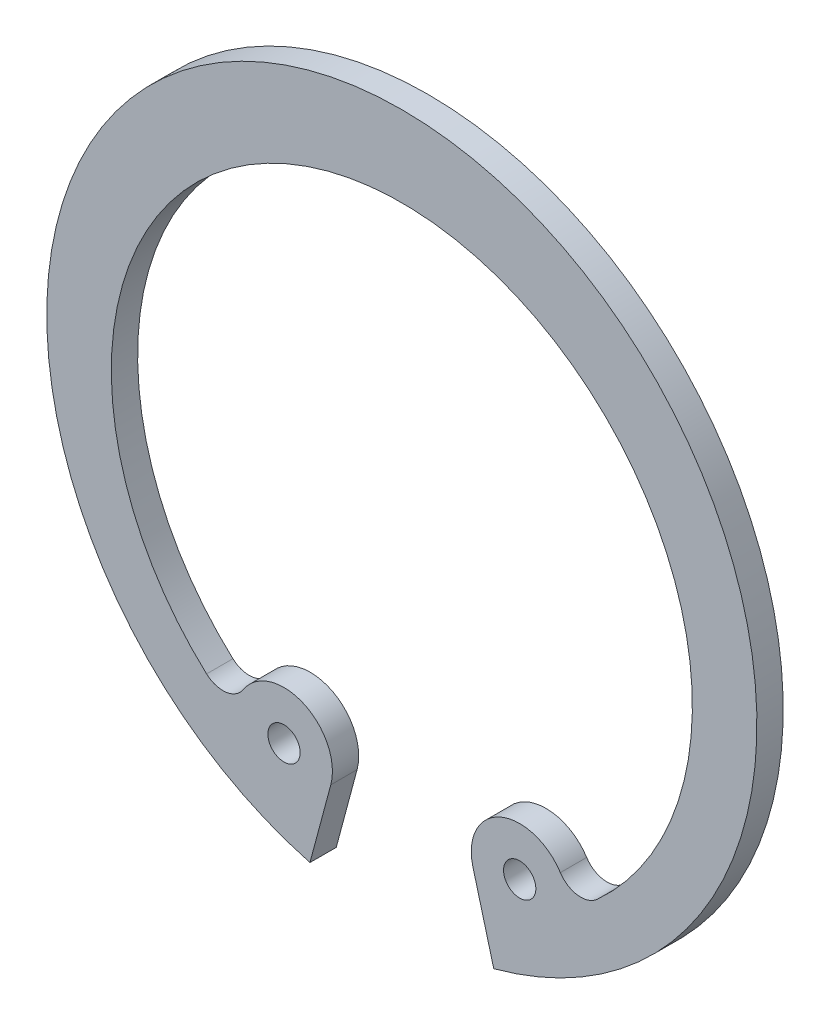
SolidWorks part; units mm, degrees
ref_plane "Face" through (0, 0, 0) normal (0, 0, 1) x (1, 0, 0)
ref_plane "Dessus" through (0, 0, 0) normal (0, 1, 0) x (1, 0, 0)
ref_plane "Droite" through (0, 0, 0) normal (1, 0, 0) x (0, 0, -1)
sketch "Esquisse1" plane through (0, 0, 0) normal (0, 0, 1) x (1, 0, 0)
  line L0 (0, 17) -> (0, -15) construction
  line L1 (-3.4941, -13.04) -> (-2.7022, -10.0846)
  line L2 (0, 0) -> (-9.5131, -9.5131) construction
  line L3 (0, 0) -> (-4.4803, -9.6081) construction
  line L4 (3.4941, -13.04) -> (2.7022, -10.0846)
  arc A0 (3.4941, -13.04) -> (-3.4941, -13.04) centre (0, 0) ccw
  arc A1 (7.4234, -8.7926) -> (-7.4234, -8.7926) centre (0, -0.6136) ccw
  circle A2 centre (-4.4803, -9.6081) radius 0.6136
  arc A3 (-2.7022, -10.0846) -> (-6.0269, -8.6096) centre (-4.4803, -9.6081) ccw
  arc A4 (-7.4234, -8.7926) -> (-6.0269, -8.6096) centre (-6.8028, -8.1088) ccw
  arc A5 (7.4234, -8.7926) -> (6.0269, -8.6096) centre (6.8028, -8.1088) cw
  arc A6 (2.7022, -10.0846) -> (6.0269, -8.6096) centre (4.4803, -9.6081) cw
  circle A7 centre (4.4803, -9.6081) radius 0.6136
  point P7 (0, 10.4318)
  point P8 (0, 13.5)
  dimension "D1" = 27
  dimension "D2" = 3.6818
  dimension "D5" = 1.2273
  dimension "D4" = 15
  dimension "D6" = 25
  dimension "D7" = 22.0909
  dimension "D3" = 3.0682
  dimension "D8" = 45
extrude "Base-Extrusion" add sketch "Esquisse1" along normal blind 1
equation "\"D7@Esquisse1\" = \"D1@Esquisse1\"*18/22"
equation "\"D3@Esquisse1\" = \"D1@Esquisse1\"*2.5/22"
equation "\"D2@Esquisse1\" = \"D1@Esquisse1\"*3/22"
equation "\"D5@Esquisse1\" = \"D1@Esquisse1\"*1/22"
